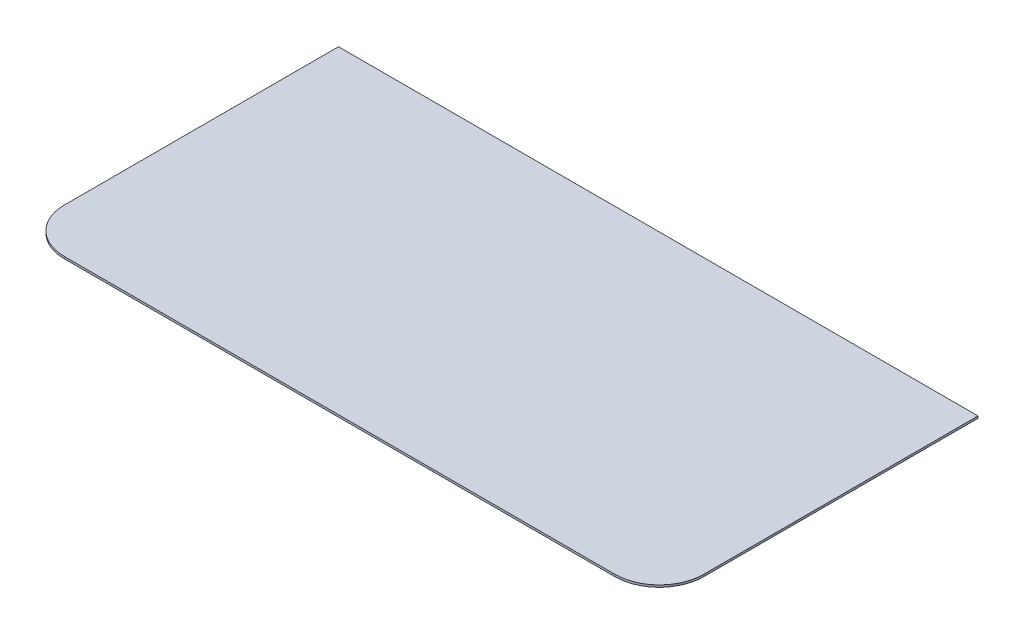
SolidWorks part; units mm, degrees
ref_plane "Ebene vorne" through (0, 0, 0) normal (0, 0, 1) x (1, 0, 0)
ref_plane "Ebene oben" through (0, 0, 0) normal (0, 1, 0) x (1, 0, 0)
ref_plane "Ebene rechts" through (0, 0, 0) normal (1, 0, 0) x (0, 0, -1)
sketch "Skizze1" plane through (0, 0, 0) normal (0, 1, 0) x (1, 0, 0)
  line L0 (0, 0) -> (0, 150.5)
  line L2 (151, 150.5) -> (151, 0)
  line L3 (0, 0) -> (151, 0)
  line L6 (151, 150.5) -> (0, 150.5)
  dimension "D1" = 151
  dimension "D2" = 150.5
extrude "Linear austragen1" add sketch "Skizze1" along normal blind 1
fillet "Verrundung1" radius 21 1 edges at (151, 0.5, 0)
mirror "Spiegeln1" about plane through (0, 1, 0) normal (1, 0, 0) of "Linear austragen1", "Verrundung1"
